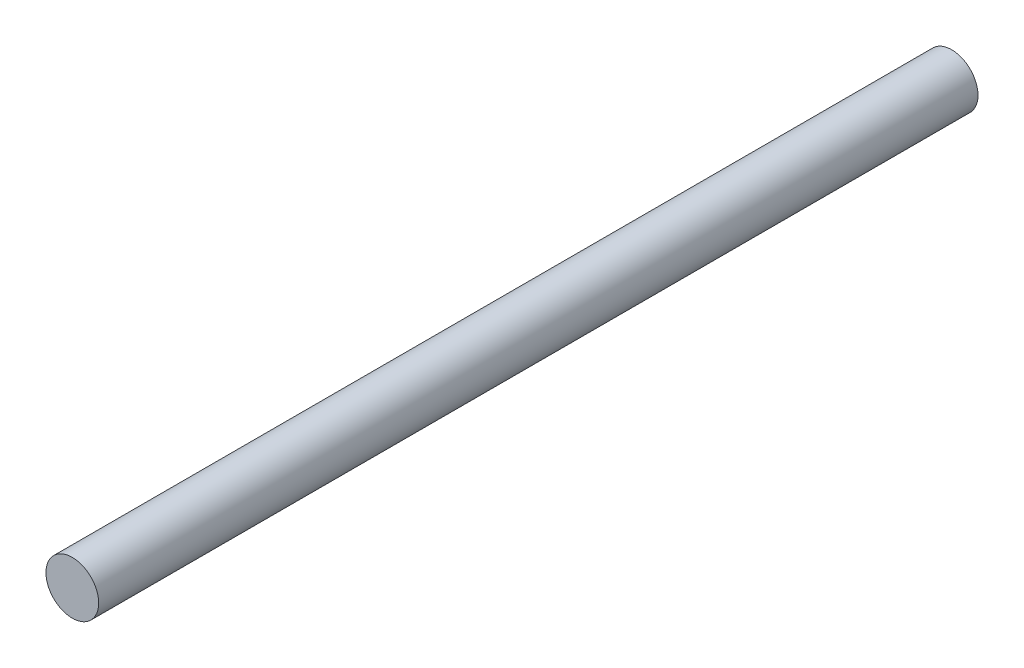
SolidWorks part; units mm, degrees
material "Plain Carbon Steel"
ref_plane "Front Plane" through (0, 0, 0) normal (0, 0, 1) x (1, 0, 0)
ref_plane "Top Plane" through (0, 0, 0) normal (0, 1, 0) x (1, 0, 0)
ref_plane "Right Plane" through (0, 0, 0) normal (1, 0, 0) x (0, 0, -1)
sketch "Sketch1" plane through (0, 0, 0) normal (0, 0, 1) x (1, 0, 0)
  circle A0 centre (0, 0) radius 2.998
  dimension "D1" = 5.996
extrude "Boss-Extrude1" add sketch "Sketch1" along normal blind 100
